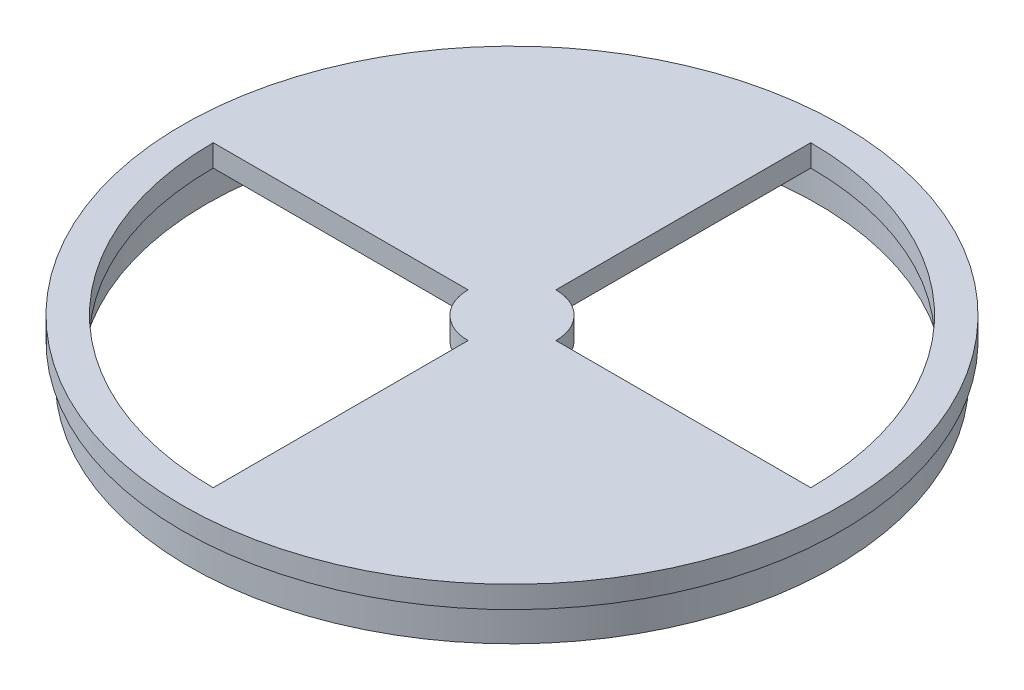
SolidWorks part; units mm, degrees
ref_plane "Alzado" through (0, 0, 0) normal (0, 0, 1) x (1, 0, 0)
ref_plane "Planta" through (0, 0, 0) normal (0, 1, 0) x (1, 0, 0)
ref_plane "Vista lateral" through (0, 0, 0) normal (1, 0, 0) x (0, 0, -1)
sketch "Croquis1" plane through (0, 0, 0) normal (0, 1, 0) x (1, 0, 0)
  line L0 (13.5413, 41.6268) -> (13.5413, 11.6268)
  line L1 (48.5413, 6.6268) -> (18.5413, 6.6268)
  line L2 (8.5413, 6.6268) -> (-21.4587, 6.6268)
  line L3 (13.5413, 1.6268) -> (13.5413, -28.3732)
  arc A0 (-21.4587, 6.6268) -> (13.5413, -28.3732) centre (13.5413, 6.6268) ccw
  circle A1 centre (13.5413, 6.6268) radius 37.5
  arc A2 (8.5413, 6.6268) -> (13.5413, 1.6268) centre (13.5413, 6.6268) ccw
  arc A3 (48.5413, 6.6268) -> (13.5413, 41.6268) centre (13.5413, 6.6268) ccw
  arc A4 (18.5413, 6.6268) -> (13.5413, 11.6268) centre (13.5413, 6.6268) ccw
extrude "Saliente-Extruir1" add sketch "Croquis1" along normal blind 2.5
sketch "Croquis2" plane through (0, 0, 0) normal (0, -1, 0) x (-1, 0, 0)
  point P0 (-13.5413, 6.6268)
ref_plane "Plano1" through (0, 0, -6.6268) normal (0, 0, 1) x (1, 0, 0)
sketch "Croquis3" plane through (0, 0, -6.6268) normal (0, 0, 1) x (1, 0, 0)
  line L0 (-22.7087, 0.1) -> (-21.2087, 0.1) construction
  line L2 (-22.7087, 0) -> (-22.7087, 0.1) construction
  line L3 (-22.7087, 0.1) -> (-22.7087, -3.9) construction
  line L9 (-22.7087, 0.1) -> (-23.2087, 0.1) construction
  line L10 (-22.7087, -3.9) -> (-22.7087, -1.182) construction
  line L12 (-21.2087, 0.1) -> (-21.2087, -3.9) construction
  line L14 (-23.2087, 0.1) -> (-21.2087, 0.1)
  line L15 (-23.2087, 0.1) -> (-23.2087, -3.9)
  line L16 (-23.2087, -3.9) -> (-21.2087, -3.9)
  line L17 (-21.2087, 0.1) -> (-21.2087, -3.9)
ref_plane "Plano2" through (0, 0, 0) normal (0, -1, 0) x (-1, 0, 0)
sketch "Croquis4" plane through (0, 0, 0) normal (0, -1, 0) x (-1, 0, 0)
  circle A0 centre (-13.5413, 6.6268) radius 36.25
sweep "Barrer1" add profiles "Croquis3" path "Croquis4"
sketch "Croquis5" plane through (0, 0, 0) normal (0, -1, 0) x (1, 0, 0)
  circle A0 centre (13.5413, -6.6268) radius 35
  circle A1 centre (13.5413, -6.6268) radius 34
  dimension "D1" = 1
extrude "Saliente-Extruir2" add sketch "Croquis5" against normal up to surface (2.5 mm away) up to face at (13.5413, 2.5, 30.8732)
